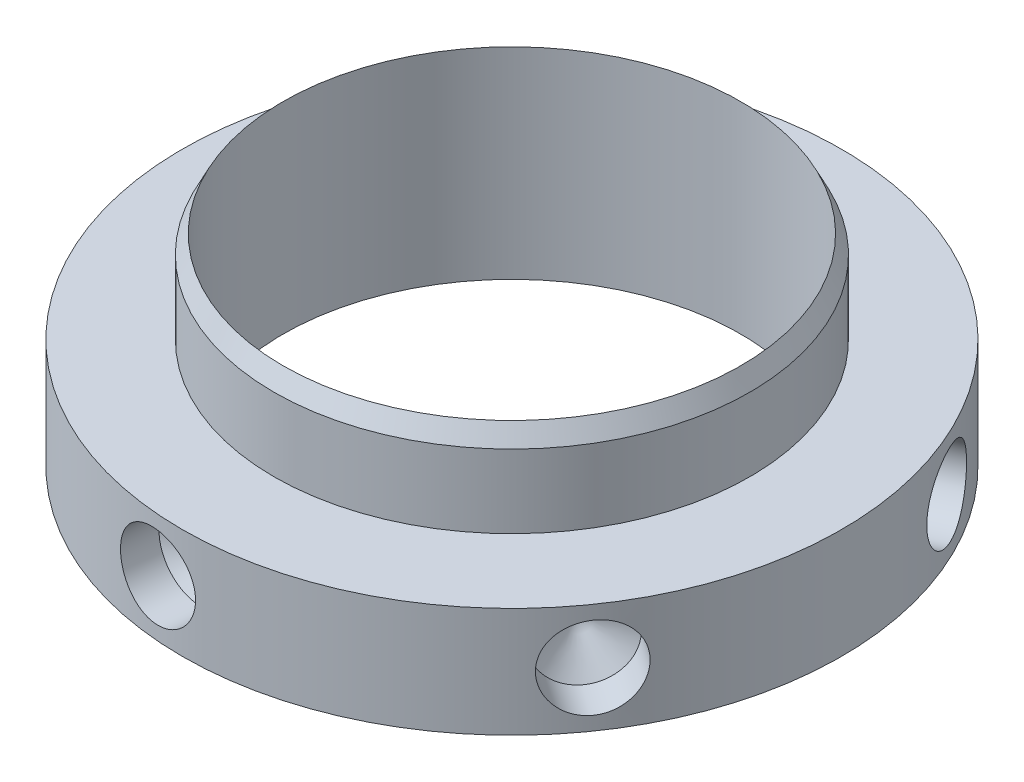
SolidWorks part; units mm, degrees
material "6061 Alloy"
ref_plane "Front" through (0, 0, 0) normal (0, 0, 1) x (1, 0, 0)
ref_plane "Top" through (0, 0, 0) normal (0, 1, 0) x (1, 0, 0)
ref_plane "Right" through (0, 0, 0) normal (1, 0, 0) x (0, 0, -1)
sketch "Sketch1" plane through (0, 0, 0) normal (1, 0, 0) x (0, 0, -1)
  line L0 (19.8438, 0) -> (28.575, 0)
  line L1 (28.575, 0) -> (28.575, 9.525)
  line L2 (28.575, 9.525) -> (20.6375, 9.525)
  line L3 (20.6375, 9.525) -> (20.6375, 15.875)
  line L4 (20.6375, 15.875) -> (19.8438, 17.4625)
  line L5 (19.8438, 17.4625) -> (19.8438, 0)
  line L6 (0, 73.5842) -> (0, -37.5192) construction
  dimension "D1" = 0.7937
  dimension "D2" = 28.575
  dimension "D3" = 17.4625
  dimension "D4" = 1.5875
  dimension "D5" = 9.525
  dimension "D6" = 20.6375
revolve "Revolve1" add sketch "Sketch1" angle 360 about L6
hole_wizard "9/32 (0.28125) Diameter Hole1" positions "3DSketch1" profile "Sketch2" hole size "9/32" standard "Ansi Inch"
sketch3d "3DSketch1"
  point P0 (23.4259, 4.7625, 16.3633)
  dimension "D1" = 4.7625
sketch "Sketch2" plane through (23.4259, 4.7625, 16.3633) normal (0, 1, 0) x (0.5726, 0, -0.8198)
  line L0 (0, 0) -> (0, 5.4482)
  line L1 (0, 5.4482) -> (3.5719, 3.302)
  line L2 (3.5719, 3.302) -> (3.5719, 0)
  line L5 (3.5719, 0) -> (0, 0)
  line L10 (0, 5.4482) -> (-3.5719, 3.302) construction
  line L11 (0, -6.35) -> (0, 107.95) construction
  dimension "Hole Dia." = 7.1437
  dimension "Hole Depth" = 3.302
  dimension "Drill Angle" = 118
pattern_circular "CirPattern1" count 6 over 360 about axis through (0, 73.5842, 0) along (0, 1, 0) of "9/32 (0.28125) Diameter Hole1"
